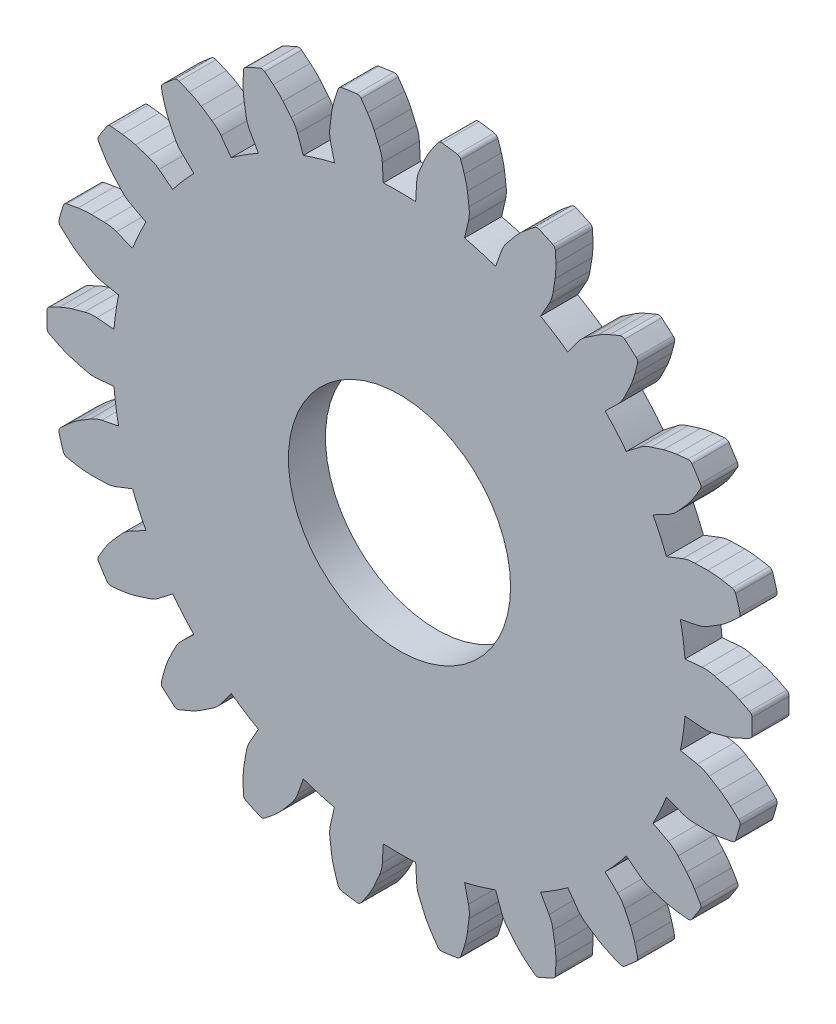
SolidWorks part; units mm, degrees
ref_plane "Front Plane" through (0, 0, 0) normal (0, 0, 1) x (1, 0, 0)
ref_plane "Top Plane" through (0, 0, 0) normal (0, 1, 0) x (1, 0, 0)
ref_plane "Right Plane" through (0, 0, 0) normal (1, 0, 0) x (0, 0, -1)
sketch "Model" plane through (0, 0, 0) normal (0, 0, 1) x (1, 0, 0)
  line L0 (38.3099, 23.5049) -> (39.2377, 23.5852)
  line L1 (38.3099, 20.8365) -> (39.2377, 20.7563)
  line L2 (38.0612, 19.1064) -> (38.974, 18.922)
  line L3 (37.3094, 16.5461) -> (38.177, 16.2077)
  line L4 (36.5833, 14.9561) -> (37.4072, 14.5221)
  line L5 (35.1407, 12.7114) -> (35.8778, 12.1423)
  line L6 (33.996, 11.3904) -> (34.6642, 10.7418)
  line L7 (31.9794, 9.643) -> (32.5263, 8.8892)
  line L8 (30.5089, 8.698) -> (30.9674, 7.8874)
  line L9 (28.0817, 7.5895) -> (28.3941, 6.7122)
  line L10 (26.4046, 7.097) -> (26.6161, 6.1901)
  line L11 (23.7634, 6.7173) -> (23.816, 5.7875)
  line L12 (22.0154, 6.7173) -> (21.9628, 5.7875)
  line L13 (19.3743, 7.097) -> (19.1628, 6.1901)
  line L14 (17.6971, 7.5895) -> (17.3847, 6.7122)
  line L15 (15.2699, 8.698) -> (14.8115, 7.8874)
  line L16 (13.7994, 9.643) -> (13.2525, 8.8892)
  line L17 (11.7828, 11.3904) -> (11.1146, 10.7418)
  line L18 (10.6382, 12.7114) -> (9.901, 12.1423)
  line L19 (9.1955, 14.9561) -> (8.3716, 14.5221)
  line L20 (8.4694, 16.5461) -> (7.6018, 16.2077)
  line L21 (7.7177, 19.1064) -> (6.8048, 18.922)
  line L22 (7.4689, 20.8365) -> (6.5411, 20.7563)
  line L23 (7.4689, 23.5049) -> (6.5411, 23.5852)
  line L24 (7.7177, 25.2351) -> (6.8048, 25.4194)
  line L25 (8.4694, 27.7953) -> (7.6018, 28.1337)
  line L26 (9.1955, 29.3853) -> (8.3716, 29.8194)
  line L27 (10.6382, 31.6301) -> (9.901, 32.1992)
  line L28 (11.7828, 32.9511) -> (11.1146, 33.5997)
  line L29 (13.7994, 34.6985) -> (13.2525, 35.4522)
  line L30 (15.2699, 35.6435) -> (14.8115, 36.4541)
  line L31 (17.6971, 36.7519) -> (17.3847, 37.6292)
  line L32 (19.3743, 37.2444) -> (19.1628, 38.1513)
  line L33 (22.0154, 37.6241) -> (21.9628, 38.5539)
  line L34 (23.7634, 37.6241) -> (23.816, 38.5539)
  line L35 (26.4046, 37.2444) -> (26.6161, 38.1513)
  line L36 (28.0817, 36.7519) -> (28.3941, 37.6292)
  line L37 (30.5089, 35.6435) -> (30.9674, 36.4541)
  line L38 (31.9794, 34.6985) -> (32.5263, 35.4522)
  line L39 (33.996, 32.9511) -> (34.6642, 33.5997)
  line L40 (35.1407, 31.6301) -> (35.8778, 32.1992)
  line L41 (36.5833, 29.3853) -> (37.4072, 29.8194)
  line L42 (37.3094, 27.7953) -> (38.177, 28.1337)
  line L43 (38.0612, 25.2351) -> (38.974, 25.4194)
  arc A0 (38.3099, 23.5049) -> (38.21, 24.3735) centre (22.8894, 22.1707) ccw
  arc A1 (39.9059, 23.5149) -> (39.2377, 23.5852) centre (39.3902, 21.8221) ccw
  arc A2 (40.5811, 23.3316) -> (39.9059, 23.5149) centre (-523.4012, -2052.5496) ccw
  arc A3 (41.2574, 23.067) -> (40.5811, 23.3316) centre (39.2009, 18.8072) ccw
  arc A4 (41.7987, 22.7989) -> (41.2574, 23.067) centre (28.9051, -2.548) ccw
  arc A5 (41.9394, 22.1707) -> (41.935, 22.582) centre (22.8894, 22.1707) ccw
  arc A6 (41.935, 22.582) -> (41.7987, 22.7989) centre (41.6857, 22.5766) ccw
  arc A7 (38.21, 19.968) -> (38.3099, 20.8365) centre (22.8894, 22.1707) ccw
  arc A8 (39.2377, 20.7563) -> (39.9059, 20.8265) centre (39.3902, 22.5193) ccw
  arc A9 (39.9059, 20.8265) -> (40.5811, 21.0098) centre (-523.4012, 2096.8911) ccw
  arc A10 (40.5811, 21.0098) -> (41.2574, 21.2744) centre (39.2009, 25.5343) ccw
  arc A11 (41.2574, 21.2744) -> (41.7987, 21.5426) centre (28.9051, 46.8895) ccw
  arc A12 (41.935, 21.7595) -> (41.9394, 22.1707) centre (22.8894, 22.1707) ccw
  arc A13 (41.7987, 21.5426) -> (41.935, 21.7595) centre (41.6857, 21.7648) ccw
  arc A14 (38.0612, 19.1064) -> (38.21, 19.968) centre (22.8894, 22.1707) ccw
  arc A15 (39.5954, 18.6664) -> (38.974, 18.922) centre (38.6236, 17.1874) ccw
  arc A16 (40.1915, 18.3003) -> (39.5954, 18.6664) centre (-1085.7889, -1814.601) ccw
  arc A17 (40.7659, 17.8558) -> (40.1915, 18.3003) centre (37.5925, 14.3479) ccw
  arc A18 (41.2097, 17.446) -> (40.7659, 17.8558) centre (21.6974, -3.2416) ccw
  arc A19 (41.1678, 16.8037) -> (41.2794, 17.1996) centre (22.8894, 22.1707) ccw
  arc A20 (41.2794, 17.1996) -> (41.2097, 17.446) centre (41.0386, 17.2646) ccw
  arc A21 (36.9688, 15.7409) -> (37.3094, 16.5461) centre (22.8894, 22.1707) ccw
  arc A22 (38.177, 16.2077) -> (38.8379, 16.0869) centre (38.82, 17.8564) ccw
  arc A23 (38.8379, 16.0869) -> (39.5374, 16.0725) centre (83.2436, 2166.7582) ccw
  arc A24 (39.5374, 16.0725) -> (40.2609, 16.1359) centre (39.4878, 20.8026) ccw
  arc A25 (40.2609, 16.1359) -> (40.8558, 16.2407) centre (35.6255, 44.1934) ccw
  arc A26 (41.0476, 16.4104) -> (41.1678, 16.8037) centre (22.8894, 22.1707) ccw
  arc A27 (40.8558, 16.2407) -> (41.0476, 16.4104) centre (40.8099, 16.4858) ccw
  arc A28 (36.5833, 14.9561) -> (36.9688, 15.7409) centre (22.8894, 22.1707) ccw
  arc A29 (37.9314, 14.1017) -> (37.4072, 14.5221) centre (36.5823, 12.9564) ccw
  arc A30 (38.4002, 13.5825) -> (37.9314, 14.1017) centre (-1558.358, -1427.8481) ccw
  arc A31 (38.8261, 12.9942) -> (38.4002, 13.5825) centre (34.793, 10.5225) ccw
  arc A32 (39.1365, 12.476) -> (38.8261, 12.9942) centre (14.5862, -1.8764) ccw
  arc A33 (38.9153, 11.8715) -> (39.1339, 12.2199) centre (22.8894, 22.1707) ccw
  arc A34 (39.1339, 12.2199) -> (39.1365, 12.476) centre (38.9213, 12.3501) ccw
  arc A35 (34.587, 12.0347) -> (35.1407, 12.7114) centre (22.8894, 22.1707) ccw
  arc A36 (35.8778, 12.1423) -> (36.4779, 11.8401) centre (36.9592, 13.543) ccw
  arc A37 (36.4779, 11.8401) -> (37.1449, 11.6293) centre (684.999, 2062.8836) ccw
  arc A38 (37.1449, 11.6293) -> (37.857, 11.4862) centre (38.4299, 16.1817) ccw
  arc A39 (37.857, 11.4862) -> (38.4573, 11.4192) centre (41.3141, 39.7131) ccw
  arc A40 (38.6892, 11.5279) -> (38.9153, 11.8715) centre (22.8894, 22.1707) ccw
  arc A41 (38.4573, 11.4192) -> (38.6892, 11.5279) centre (38.4824, 11.6673) ccw
  arc A42 (33.996, 11.3904) -> (34.587, 12.0347) centre (22.8894, 22.1707) ccw
  arc A43 (35.0487, 10.1908) -> (34.6642, 10.7418) centre (33.4317, 9.4719) ccw
  arc A44 (35.3523, 9.5605) -> (35.0487, 10.1908) centre (-1902.8239, -923.6232) ccw
  arc A45 (35.5953, 8.8761) -> (35.3523, 9.5605) centre (31.0291, 7.6407) ccw
  arc A46 (35.7471, 8.2914) -> (35.5953, 8.8761) centre (8.1477, 1.437) ccw
  arc A47 (35.3645, 7.7737) -> (35.6724, 8.0464) centre (22.8894, 22.1707) ccw
  arc A48 (35.6724, 8.0464) -> (35.7471, 8.2914) centre (35.5051, 8.2312) ccw
  arc A49 (31.2575, 9.1497) -> (31.9794, 9.643) centre (22.8894, 22.1707) ccw
  arc A50 (32.5263, 8.8892) -> (33.017, 8.4302) centre (33.9586, 9.9285) ccw
  arc A51 (33.017, 8.4302) -> (33.5976, 8.04) centre (1233.1141, 1793.6825) ccw
  arc A52 (33.5976, 8.04) -> (34.2405, 7.7022) centre (36.1131, 12.046) ccw
  arc A53 (34.2405, 7.7022) -> (34.7977, 7.4687) centre (45.51, 33.8117) ccw
  arc A54 (35.0508, 7.5077) -> (35.3645, 7.7737) centre (22.8894, 22.1707) ccw
  arc A55 (34.7977, 7.4687) -> (35.0508, 7.5077) centre (34.8916, 7.6997) ccw
  arc A56 (30.5089, 8.698) -> (31.2575, 9.1497) centre (22.8894, 22.1707) ccw
  arc A57 (31.1811, 7.2503) -> (30.9674, 7.8874) centre (29.427, 7.0162) ccw
  arc A58 (31.2948, 6.5601) -> (31.1811, 7.2503) centre (-2091.2799, -342.7758) ccw
  arc A59 (31.335, 5.8349) -> (31.2948, 6.5601) centre (26.6058, 5.936) ccw
  arc A60 (31.316, 5.2311) -> (31.335, 5.8349) centre (2.9034, 6.4301) ccw
  arc A61 (30.8031, 4.8422) -> (31.1753, 5.0171) centre (22.8894, 22.1707) ccw
  arc A62 (31.1753, 5.0171) -> (31.316, 5.2311) centre (31.0668, 5.2416) ccw
  arc A63 (27.2501, 7.3196) -> (28.0817, 7.5895) centre (22.8894, 22.1707) ccw
  arc A64 (28.3941, 6.7122) -> (28.7356, 6.1335) centre (30.0612, 7.3059) ccw
  arc A65 (28.7356, 6.1335) -> (29.1828, 5.5956) centre (1683.1841, 1380.9642) ccw
  arc A66 (29.1828, 5.5956) -> (29.7044, 5.0903) centre (32.725, 8.7306) ccw
  arc A67 (29.7044, 5.0903) -> (30.1733, 4.7093) centre (47.8734, 26.9672) ccw
  arc A68 (30.4271, 4.6754) -> (30.8031, 4.8422) centre (22.8894, 22.1707) ccw
  arc A69 (30.1733, 4.7093) -> (30.4271, 4.6754) centre (30.3285, 4.9044) ccw
  arc A70 (26.4046, 7.097) -> (27.2501, 7.3196) centre (22.8894, 22.1707) ccw
  arc A71 (26.6416, 5.5187) -> (26.6161, 6.1901) centre (24.8926, 5.7883) ccw
  arc A72 (26.5563, 4.8244) -> (26.6416, 5.5187) centre (-2108.4585, 267.6374) ccw
  arc A73 (26.3906, 4.1172) -> (26.5563, 4.8244) centre (21.8815, 5.5466) ccw
  arc A74 (26.2022, 3.5433) -> (26.3906, 4.1172) centre (-0.7216, 12.6984) ccw
  arc A75 (25.6005, 3.3146) -> (26.0069, 3.3775) centre (22.8894, 22.1707) ccw
  arc A76 (26.0069, 3.3775) -> (26.2022, 3.5433) centre (25.9661, 3.6235) ccw
  arc A77 (22.8894, 6.6926) -> (23.7634, 6.7173) centre (22.8894, 22.1707) ccw
  arc A78 (23.816, 5.7875) -> (23.9806, 5.1361) centre (25.5828, 5.8875) ccw
  arc A79 (23.9806, 5.1361) -> (24.2581, 4.4939) centre (1998.7468, 858.1644) ccw
  arc A80 (24.2581, 4.4939) -> (24.6163, 3.8621) centre (28.5401, 6.504) ccw
  arc A81 (24.6163, 3.8621) -> (24.9587, 3.3645) centre (48.2127, 19.7341) ccw
  arc A82 (25.1928, 3.2605) -> (25.6005, 3.3146) centre (22.8894, 22.1707) ccw
  arc A83 (24.9587, 3.3645) -> (25.1928, 3.2605) centre (25.1627, 3.508) ccw
  arc A84 (22.0154, 6.7173) -> (22.8894, 6.6926) centre (22.8894, 22.1707) ccw
  arc A85 (21.7982, 5.1361) -> (21.9628, 5.7875) centre (20.196, 5.8875) ccw
  arc A86 (21.5207, 4.4939) -> (21.7982, 5.1361) centre (-1952.968, 858.1644) ccw
  arc A87 (21.1625, 3.8621) -> (21.5207, 4.4939) centre (17.2387, 6.504) ccw
  arc A88 (20.8201, 3.3645) -> (21.1625, 3.8621) centre (-2.4339, 19.7341) ccw
  arc A89 (20.1783, 3.3146) -> (20.586, 3.2605) centre (22.8894, 22.1707) ccw
  arc A90 (20.586, 3.2605) -> (20.8201, 3.3645) centre (20.6162, 3.508) ccw
  arc A91 (18.5287, 7.3196) -> (19.3743, 7.097) centre (22.8894, 22.1707) ccw
  arc A92 (19.1628, 6.1901) -> (19.1372, 5.5187) centre (20.8862, 5.7883) ccw
  arc A93 (19.1372, 5.5187) -> (19.2225, 4.8244) centre (2154.2373, 267.6374) ccw
  arc A94 (19.2225, 4.8244) -> (19.3882, 4.1172) centre (23.8974, 5.5466) ccw
  arc A95 (19.3882, 4.1172) -> (19.5766, 3.5433) centre (46.5004, 12.6984) ccw
  arc A96 (19.7719, 3.3775) -> (20.1783, 3.3146) centre (22.8894, 22.1707) ccw
  arc A97 (19.5766, 3.5433) -> (19.7719, 3.3775) centre (19.8127, 3.6235) ccw
  arc A98 (17.6971, 7.5895) -> (18.5287, 7.3196) centre (22.8894, 22.1707) ccw
  arc A99 (17.0432, 6.1335) -> (17.3847, 6.7122) centre (15.7176, 7.3059) ccw
  arc A100 (16.596, 5.5956) -> (17.0432, 6.1335) centre (-1637.4053, 1380.9642) ccw
  arc A101 (16.0744, 5.0903) -> (16.596, 5.5956) centre (13.0538, 8.7306) ccw
  arc A102 (15.6056, 4.7093) -> (16.0744, 5.0903) centre (-2.0946, 26.9672) ccw
  arc A103 (14.9758, 4.8422) -> (15.3517, 4.6754) centre (22.8894, 22.1707) ccw
  arc A104 (15.3517, 4.6754) -> (15.6056, 4.7093) centre (15.4504, 4.9044) ccw
  arc A105 (14.5213, 9.1497) -> (15.2699, 8.698) centre (22.8894, 22.1707) ccw
  arc A106 (14.8115, 7.8874) -> (14.5978, 7.2503) centre (16.3518, 7.0162) ccw
  arc A107 (14.5978, 7.2503) -> (14.484, 6.5601) centre (2137.0587, -342.7758) ccw
  arc A108 (14.484, 6.5601) -> (14.4438, 5.8349) centre (19.173, 5.936) ccw
  arc A109 (14.4438, 5.8349) -> (14.4628, 5.2311) centre (42.8754, 6.4301) ccw
  arc A110 (14.6035, 5.0171) -> (14.9758, 4.8422) centre (22.8894, 22.1707) ccw
  arc A111 (14.4628, 5.2311) -> (14.6035, 5.0171) centre (14.712, 5.2416) ccw
  arc A112 (13.7994, 9.643) -> (14.5213, 9.1497) centre (22.8894, 22.1707) ccw
  arc A113 (12.7618, 8.4302) -> (13.2525, 8.8892) centre (11.8202, 9.9285) ccw
  arc A114 (12.1812, 8.04) -> (12.7618, 8.4302) centre (-1187.3353, 1793.6825) ccw
  arc A115 (11.5383, 7.7022) -> (12.1812, 8.04) centre (9.6657, 12.046) ccw
  arc A116 (10.9812, 7.4687) -> (11.5383, 7.7022) centre (0.2688, 33.8117) ccw
  arc A117 (10.4143, 7.7737) -> (10.728, 7.5077) centre (22.8894, 22.1707) ccw
  arc A118 (10.728, 7.5077) -> (10.9812, 7.4687) centre (10.8872, 7.6997) ccw
  arc A119 (11.1918, 12.0347) -> (11.7828, 11.3904) centre (22.8894, 22.1707) ccw
  arc A120 (11.1146, 10.7418) -> (10.7301, 10.1908) centre (12.3472, 9.4719) ccw
  arc A121 (10.7301, 10.1908) -> (10.4265, 9.5605) centre (1948.6027, -923.6232) ccw
  arc A122 (10.4265, 9.5605) -> (10.1836, 8.8761) centre (14.7497, 7.6407) ccw
  arc A123 (10.1836, 8.8761) -> (10.0317, 8.2914) centre (37.6312, 1.437) ccw
  arc A124 (10.1064, 8.0464) -> (10.4143, 7.7737) centre (22.8894, 22.1707) ccw
  arc A125 (10.0317, 8.2914) -> (10.1064, 8.0464) centre (10.2737, 8.2312) ccw
  arc A126 (10.6382, 12.7114) -> (11.1918, 12.0347) centre (22.8894, 22.1707) ccw
  arc A127 (9.3009, 11.8401) -> (9.901, 12.1423) centre (8.8196, 13.543) ccw
  arc A128 (8.6339, 11.6293) -> (9.3009, 11.8401) centre (-639.2201, 2062.8836) ccw
  arc A129 (7.9218, 11.4862) -> (8.6339, 11.6293) centre (7.3489, 16.1817) ccw
  arc A130 (7.3215, 11.4192) -> (7.9218, 11.4862) centre (4.4647, 39.7131) ccw
  arc A131 (6.8635, 11.8715) -> (7.0896, 11.5279) centre (22.8894, 22.1707) ccw
  arc A132 (7.0896, 11.5279) -> (7.3215, 11.4192) centre (7.2964, 11.6673) ccw
  arc A133 (8.81, 15.7409) -> (9.1955, 14.9561) centre (22.8894, 22.1707) ccw
  arc A134 (8.3716, 14.5221) -> (7.8475, 14.1017) centre (9.1965, 12.9564) ccw
  arc A135 (7.8475, 14.1017) -> (7.3786, 13.5825) centre (1604.1368, -1427.8481) ccw
  arc A136 (7.3786, 13.5825) -> (6.9527, 12.9942) centre (10.9858, 10.5225) ccw
  arc A137 (6.9527, 12.9942) -> (6.6423, 12.476) centre (31.1927, -1.8764) ccw
  arc A138 (6.6449, 12.2199) -> (6.8635, 11.8715) centre (22.8894, 22.1707) ccw
  arc A139 (6.6423, 12.476) -> (6.6449, 12.2199) centre (6.8576, 12.3501) ccw
  arc A140 (8.4694, 16.5461) -> (8.81, 15.7409) centre (22.8894, 22.1707) ccw
  arc A141 (6.9409, 16.0869) -> (7.6018, 16.2077) centre (6.9588, 17.8564) ccw
  arc A142 (6.2415, 16.0725) -> (6.9409, 16.0869) centre (-37.4648, 2166.7582) ccw
  arc A143 (5.518, 16.1359) -> (6.2415, 16.0725) centre (6.2911, 20.8026) ccw
  arc A144 (4.923, 16.2407) -> (5.518, 16.1359) centre (10.1533, 44.1934) ccw
  arc A145 (4.6111, 16.8037) -> (4.7312, 16.4104) centre (22.8894, 22.1707) ccw
  arc A146 (4.7312, 16.4104) -> (4.923, 16.2407) centre (4.9689, 16.4858) ccw
  arc A147 (7.5688, 19.968) -> (7.7177, 19.1064) centre (22.8894, 22.1707) ccw
  arc A148 (6.8048, 18.922) -> (6.1835, 18.6664) centre (7.1552, 17.1874) ccw
  arc A149 (6.1835, 18.6664) -> (5.5873, 18.3003) centre (1131.5677, -1814.601) ccw
  arc A150 (5.5873, 18.3003) -> (5.0129, 17.8558) centre (8.1863, 14.3479) ccw
  arc A151 (5.0129, 17.8558) -> (4.5691, 17.446) centre (24.0815, -3.2416) ccw
  arc A152 (4.4995, 17.1996) -> (4.6111, 16.8037) centre (22.8894, 22.1707) ccw
  arc A153 (4.5691, 17.446) -> (4.4995, 17.1996) centre (4.7402, 17.2646) ccw
  arc A154 (7.4689, 20.8365) -> (7.5688, 19.968) centre (22.8894, 22.1707) ccw
  arc A155 (5.8729, 20.8265) -> (6.5411, 20.7563) centre (6.3886, 22.5193) ccw
  arc A156 (5.1978, 21.0098) -> (5.8729, 20.8265) centre (569.1801, 2096.8911) ccw
  arc A157 (4.5214, 21.2744) -> (5.1978, 21.0098) centre (6.578, 25.5343) ccw
  arc A158 (3.9801, 21.5426) -> (4.5214, 21.2744) centre (16.8737, 46.8895) ccw
  arc A159 (3.8394, 22.1707) -> (3.8438, 21.7595) centre (22.8894, 22.1707) ccw
  arc A160 (3.8438, 21.7595) -> (3.9801, 21.5426) centre (4.0932, 21.7648) ccw
  arc A161 (7.5688, 24.3735) -> (7.4689, 23.5049) centre (22.8894, 22.1707) ccw
  arc A162 (6.5411, 23.5852) -> (5.8729, 23.5149) centre (6.3886, 21.8221) ccw
  arc A163 (5.8729, 23.5149) -> (5.1978, 23.3316) centre (569.1801, -2052.5496) ccw
  arc A164 (5.1978, 23.3316) -> (4.5214, 23.067) centre (6.578, 18.8072) ccw
  arc A165 (4.5214, 23.067) -> (3.9801, 22.7989) centre (16.8737, -2.548) ccw
  arc A166 (3.8438, 22.582) -> (3.8394, 22.1707) centre (22.8894, 22.1707) ccw
  arc A167 (3.9801, 22.7989) -> (3.8438, 22.582) centre (4.0932, 22.5766) ccw
  arc A168 (7.7177, 25.2351) -> (7.5688, 24.3735) centre (22.8894, 22.1707) ccw
  arc A169 (6.1835, 25.6751) -> (6.8048, 25.4194) centre (7.1552, 27.154) ccw
  arc A170 (5.5873, 26.0411) -> (6.1835, 25.6751) centre (1131.5677, 1858.9424) ccw
  arc A171 (5.0129, 26.4856) -> (5.5873, 26.0411) centre (8.1863, 29.9935) ccw
  arc A172 (4.5691, 26.8954) -> (5.0129, 26.4856) centre (24.0815, 47.583) ccw
  arc A173 (4.6111, 27.5377) -> (4.4995, 27.1419) centre (22.8894, 22.1707) ccw
  arc A174 (4.4995, 27.1419) -> (4.5691, 26.8954) centre (4.7402, 27.0768) ccw
  arc A175 (8.81, 28.6006) -> (8.4694, 27.7953) centre (22.8894, 22.1707) ccw
  arc A176 (7.6018, 28.1337) -> (6.9409, 28.2546) centre (6.9588, 26.485) ccw
  arc A177 (6.9409, 28.2546) -> (6.2415, 28.2689) centre (-37.4648, -2122.4167) ccw
  arc A178 (6.2415, 28.2689) -> (5.518, 28.2056) centre (6.2911, 23.5389) ccw
  arc A179 (5.518, 28.2056) -> (4.923, 28.1008) centre (10.1533, 0.1481) ccw
  arc A180 (4.7312, 27.9311) -> (4.6111, 27.5377) centre (22.8894, 22.1707) ccw
  arc A181 (4.923, 28.1008) -> (4.7312, 27.9311) centre (4.9689, 27.8557) ccw
  arc A182 (9.1955, 29.3853) -> (8.81, 28.6006) centre (22.8894, 22.1707) ccw
  arc A183 (7.8475, 30.2397) -> (8.3716, 29.8194) centre (9.1965, 31.385) ccw
  arc A184 (7.3786, 30.7589) -> (7.8475, 30.2397) centre (1604.1368, 1472.1895) ccw
  arc A185 (6.9527, 31.3472) -> (7.3786, 30.7589) centre (10.9858, 33.819) ccw
  arc A186 (6.6423, 31.8654) -> (6.9527, 31.3472) centre (31.1927, 46.2178) ccw
  arc A187 (6.8635, 32.4699) -> (6.6449, 32.1216) centre (22.8894, 22.1707) ccw
  arc A188 (6.6449, 32.1216) -> (6.6423, 31.8654) centre (6.8576, 31.9913) ccw
  arc A189 (11.1918, 32.3067) -> (10.6382, 31.6301) centre (22.8894, 22.1707) ccw
  arc A190 (9.901, 32.1992) -> (9.3009, 32.5014) centre (8.8196, 30.7984) ccw
  arc A191 (9.3009, 32.5014) -> (8.6339, 32.7122) centre (-639.2201, -2018.5421) ccw
  arc A192 (8.6339, 32.7122) -> (7.9218, 32.8552) centre (7.3489, 28.1598) ccw
  arc A193 (7.9218, 32.8552) -> (7.3215, 32.9223) centre (4.4647, 4.6283) ccw
  arc A194 (7.0896, 32.8135) -> (6.8635, 32.4699) centre (22.8894, 22.1707) ccw
  arc A195 (7.3215, 32.9223) -> (7.0896, 32.8135) centre (7.2964, 32.6742) ccw
  arc A196 (11.7828, 32.9511) -> (11.1918, 32.3067) centre (22.8894, 22.1707) ccw
  arc A197 (10.7301, 34.1507) -> (11.1146, 33.5997) centre (12.3472, 34.8695) ccw
  arc A198 (10.4265, 34.7809) -> (10.7301, 34.1507) centre (1948.6027, 967.9647) ccw
  arc A199 (10.1836, 35.4654) -> (10.4265, 34.7809) centre (14.7497, 36.7008) ccw
  arc A200 (10.0317, 36.0501) -> (10.1836, 35.4654) centre (37.6312, 42.9044) ccw
  arc A201 (10.4143, 36.5677) -> (10.1064, 36.2951) centre (22.8894, 22.1707) ccw
  arc A202 (10.1064, 36.2951) -> (10.0317, 36.0501) centre (10.2737, 36.1102) ccw
  arc A203 (14.5213, 35.1917) -> (13.7994, 34.6985) centre (22.8894, 22.1707) ccw
  arc A204 (13.2525, 35.4522) -> (12.7618, 35.9112) centre (11.8202, 34.4129) ccw
  arc A205 (12.7618, 35.9112) -> (12.1812, 36.3014) centre (-1187.3353, -1749.3411) ccw
  arc A206 (12.1812, 36.3014) -> (11.5383, 36.6393) centre (9.6657, 32.2954) ccw
  arc A207 (11.5383, 36.6393) -> (10.9812, 36.8728) centre (0.2688, 10.5297) ccw
  arc A208 (10.728, 36.8337) -> (10.4143, 36.5677) centre (22.8894, 22.1707) ccw
  arc A209 (10.9812, 36.8728) -> (10.728, 36.8337) centre (10.8872, 36.6418) ccw
  arc A210 (15.2699, 35.6435) -> (14.5213, 35.1917) centre (22.8894, 22.1707) ccw
  arc A211 (14.5978, 37.0911) -> (14.8115, 36.4541) centre (16.3518, 37.3252) ccw
  arc A212 (14.484, 37.7813) -> (14.5978, 37.0911) centre (2137.0587, 387.1172) ccw
  arc A213 (14.4438, 38.5065) -> (14.484, 37.7813) centre (19.173, 38.4054) ccw
  arc A214 (14.4628, 39.1103) -> (14.4438, 38.5065) centre (42.8754, 37.9113) ccw
  arc A215 (14.9758, 39.4992) -> (14.6035, 39.3243) centre (22.8894, 22.1707) ccw
  arc A216 (14.6035, 39.3243) -> (14.4628, 39.1103) centre (14.712, 39.0998) ccw
  arc A217 (18.5287, 37.0219) -> (17.6971, 36.7519) centre (22.8894, 22.1707) ccw
  arc A218 (17.3847, 37.6292) -> (17.0432, 38.2079) centre (15.7176, 37.0356) ccw
  arc A219 (17.0432, 38.2079) -> (16.596, 38.7459) centre (-1637.4053, -1336.6227) ccw
  arc A220 (16.596, 38.7459) -> (16.0744, 39.2512) centre (13.0538, 35.6109) ccw
  arc A221 (16.0744, 39.2512) -> (15.6056, 39.6322) centre (-2.0946, 17.3742) ccw
  arc A222 (15.3517, 39.666) -> (14.9758, 39.4992) centre (22.8894, 22.1707) ccw
  arc A223 (15.6056, 39.6322) -> (15.3517, 39.666) centre (15.4504, 39.437) ccw
  arc A224 (19.3743, 37.2444) -> (18.5287, 37.0219) centre (22.8894, 22.1707) ccw
  arc A225 (19.1372, 38.8227) -> (19.1628, 38.1513) centre (20.8862, 38.5532) ccw
  arc A226 (19.2225, 39.5171) -> (19.1372, 38.8227) centre (2154.2373, -223.296) ccw
  arc A227 (19.3882, 40.2242) -> (19.2225, 39.5171) centre (23.8974, 38.7948) ccw
  arc A228 (19.5766, 40.7982) -> (19.3882, 40.2242) centre (46.5004, 31.643) ccw
  arc A229 (20.1783, 41.0268) -> (19.7719, 40.9639) centre (22.8894, 22.1707) ccw
  arc A230 (19.7719, 40.9639) -> (19.5766, 40.7982) centre (19.8127, 40.7179) ccw
  arc A231 (22.8894, 37.6488) -> (22.0154, 37.6241) centre (22.8894, 22.1707) ccw
  arc A232 (21.9628, 38.5539) -> (21.7982, 39.2053) centre (20.196, 38.454) ccw
  arc A233 (21.7982, 39.2053) -> (21.5207, 39.8475) centre (-1952.968, -813.823) ccw
  arc A234 (21.5207, 39.8475) -> (21.1625, 40.4793) centre (17.2387, 37.8375) ccw
  arc A235 (21.1625, 40.4793) -> (20.8201, 40.977) centre (-2.4339, 24.6073) ccw
  arc A236 (20.586, 41.081) -> (20.1783, 41.0268) centre (22.8894, 22.1707) ccw
  arc A237 (20.8201, 40.977) -> (20.586, 41.081) centre (20.6162, 40.8334) ccw
  arc A238 (23.7634, 37.6241) -> (22.8894, 37.6488) centre (22.8894, 22.1707) ccw
  arc A239 (23.9806, 39.2053) -> (23.816, 38.5539) centre (25.5828, 38.454) ccw
  arc A240 (24.2581, 39.8475) -> (23.9806, 39.2053) centre (1998.7468, -813.823) ccw
  arc A241 (24.6163, 40.4793) -> (24.2581, 39.8475) centre (28.5401, 37.8375) ccw
  arc A242 (24.9587, 40.977) -> (24.6163, 40.4793) centre (48.2127, 24.6073) ccw
  arc A243 (25.6005, 41.0268) -> (25.1928, 41.081) centre (22.8894, 22.1707) ccw
  arc A244 (25.1928, 41.081) -> (24.9587, 40.977) centre (25.1627, 40.8334) ccw
  arc A245 (27.2501, 37.0219) -> (26.4046, 37.2444) centre (22.8894, 22.1707) ccw
  arc A246 (26.6161, 38.1513) -> (26.6416, 38.8227) centre (24.8926, 38.5532) ccw
  arc A247 (26.6416, 38.8227) -> (26.5563, 39.5171) centre (-2108.4585, -223.296) ccw
  arc A248 (26.5563, 39.5171) -> (26.3906, 40.2242) centre (21.8815, 38.7948) ccw
  arc A249 (26.3906, 40.2242) -> (26.2022, 40.7982) centre (-0.7216, 31.643) ccw
  arc A250 (26.0069, 40.9639) -> (25.6005, 41.0268) centre (22.8894, 22.1707) ccw
  arc A251 (26.2022, 40.7982) -> (26.0069, 40.9639) centre (25.9661, 40.7179) ccw
  arc A252 (28.0817, 36.7519) -> (27.2501, 37.0219) centre (22.8894, 22.1707) ccw
  arc A253 (28.7356, 38.2079) -> (28.3941, 37.6292) centre (30.0612, 37.0356) ccw
  arc A254 (29.1828, 38.7459) -> (28.7356, 38.2079) centre (1683.1841, -1336.6227) ccw
  arc A255 (29.7044, 39.2512) -> (29.1828, 38.7459) centre (32.725, 35.6109) ccw
  arc A256 (30.1733, 39.6322) -> (29.7044, 39.2512) centre (47.8734, 17.3742) ccw
  arc A257 (30.8031, 39.4992) -> (30.4271, 39.666) centre (22.8894, 22.1707) ccw
  arc A258 (30.4271, 39.666) -> (30.1733, 39.6322) centre (30.3285, 39.437) ccw
  arc A259 (31.2575, 35.1917) -> (30.5089, 35.6435) centre (22.8894, 22.1707) ccw
  arc A260 (30.9674, 36.4541) -> (31.1811, 37.0911) centre (29.427, 37.3252) ccw
  arc A261 (31.1811, 37.0911) -> (31.2948, 37.7813) centre (-2091.2799, 387.1172) ccw
  arc A262 (31.2948, 37.7813) -> (31.335, 38.5065) centre (26.6058, 38.4054) ccw
  arc A263 (31.335, 38.5065) -> (31.316, 39.1103) centre (2.9034, 37.9113) ccw
  arc A264 (31.1753, 39.3243) -> (30.8031, 39.4992) centre (22.8894, 22.1707) ccw
  arc A265 (31.316, 39.1103) -> (31.1753, 39.3243) centre (31.0668, 39.0998) ccw
  arc A266 (31.9794, 34.6985) -> (31.2575, 35.1917) centre (22.8894, 22.1707) ccw
  arc A267 (33.017, 35.9112) -> (32.5263, 35.4522) centre (33.9586, 34.4129) ccw
  arc A268 (33.5976, 36.3014) -> (33.017, 35.9112) centre (1233.1141, -1749.3411) ccw
  arc A269 (34.2405, 36.6393) -> (33.5976, 36.3014) centre (36.1131, 32.2954) ccw
  arc A270 (34.7977, 36.8728) -> (34.2405, 36.6393) centre (45.51, 10.5297) ccw
  arc A271 (35.3645, 36.5677) -> (35.0508, 36.8337) centre (22.8894, 22.1707) ccw
  arc A272 (35.0508, 36.8337) -> (34.7977, 36.8728) centre (34.8916, 36.6418) ccw
  arc A273 (34.587, 32.3067) -> (33.996, 32.9511) centre (22.8894, 22.1707) ccw
  arc A274 (34.6642, 33.5997) -> (35.0487, 34.1507) centre (33.4317, 34.8695) ccw
  arc A275 (35.0487, 34.1507) -> (35.3523, 34.7809) centre (-1902.8239, 967.9647) ccw
  arc A276 (35.3523, 34.7809) -> (35.5953, 35.4654) centre (31.0291, 36.7008) ccw
  arc A277 (35.5953, 35.4654) -> (35.7471, 36.0501) centre (8.1477, 42.9044) ccw
  arc A278 (35.6724, 36.2951) -> (35.3645, 36.5677) centre (22.8894, 22.1707) ccw
  arc A279 (35.7471, 36.0501) -> (35.6724, 36.2951) centre (35.5051, 36.1102) ccw
  arc A280 (35.1407, 31.6301) -> (34.587, 32.3067) centre (22.8894, 22.1707) ccw
  arc A281 (36.4779, 32.5014) -> (35.8778, 32.1992) centre (36.9592, 30.7984) ccw
  arc A282 (37.1449, 32.7122) -> (36.4779, 32.5014) centre (684.999, -2018.5421) ccw
  arc A283 (37.857, 32.8552) -> (37.1449, 32.7122) centre (38.4299, 28.1598) ccw
  arc A284 (38.4573, 32.9223) -> (37.857, 32.8552) centre (41.3141, 4.6283) ccw
  arc A285 (38.9153, 32.4699) -> (38.6892, 32.8135) centre (22.8894, 22.1707) ccw
  arc A286 (38.6892, 32.8135) -> (38.4573, 32.9223) centre (38.4824, 32.6742) ccw
  arc A287 (36.9688, 28.6006) -> (36.5833, 29.3853) centre (22.8894, 22.1707) ccw
  arc A288 (37.4072, 29.8194) -> (37.9314, 30.2397) centre (36.5823, 31.385) ccw
  arc A289 (37.9314, 30.2397) -> (38.4002, 30.7589) centre (-1558.358, 1472.1895) ccw
  arc A290 (38.4002, 30.7589) -> (38.8261, 31.3472) centre (34.793, 33.819) ccw
  arc A291 (38.8261, 31.3472) -> (39.1365, 31.8654) centre (14.5862, 46.2178) ccw
  arc A292 (39.1339, 32.1216) -> (38.9153, 32.4699) centre (22.8894, 22.1707) ccw
  arc A293 (39.1365, 31.8654) -> (39.1339, 32.1216) centre (38.9213, 31.9913) ccw
  arc A294 (37.3094, 27.7953) -> (36.9688, 28.6006) centre (22.8894, 22.1707) ccw
  arc A295 (38.8379, 28.2546) -> (38.177, 28.1337) centre (38.82, 26.485) ccw
  arc A296 (39.5374, 28.2689) -> (38.8379, 28.2546) centre (83.2436, -2122.4167) ccw
  arc A297 (40.2609, 28.2056) -> (39.5374, 28.2689) centre (39.4878, 23.5389) ccw
  arc A298 (40.8558, 28.1008) -> (40.2609, 28.2056) centre (35.6255, 0.1481) ccw
  arc A299 (41.1678, 27.5377) -> (41.0476, 27.9311) centre (22.8894, 22.1707) ccw
  arc A300 (41.0476, 27.9311) -> (40.8558, 28.1008) centre (40.8099, 27.8557) ccw
  arc A301 (38.21, 24.3735) -> (38.0612, 25.2351) centre (22.8894, 22.1707) ccw
  arc A302 (38.974, 25.4194) -> (39.5954, 25.6751) centre (38.6236, 27.154) ccw
  arc A303 (39.5954, 25.6751) -> (40.1915, 26.0411) centre (-1085.7889, 1858.9424) ccw
  arc A304 (40.1915, 26.0411) -> (40.7659, 26.4856) centre (37.5925, 29.9935) ccw
  arc A305 (40.7659, 26.4856) -> (41.2097, 26.8954) centre (21.6974, 47.583) ccw
  arc A306 (41.2794, 27.1419) -> (41.1678, 27.5377) centre (22.8894, 22.1707) ccw
  arc A307 (41.2097, 26.8954) -> (41.2794, 27.1419) centre (41.0386, 27.0768) ccw
  circle A308 centre (22.8894, 22.1707) radius 6
  dimension "D1" = 12
extrude "Boss-Extrude1" add sketch "Model" along normal blind 2
